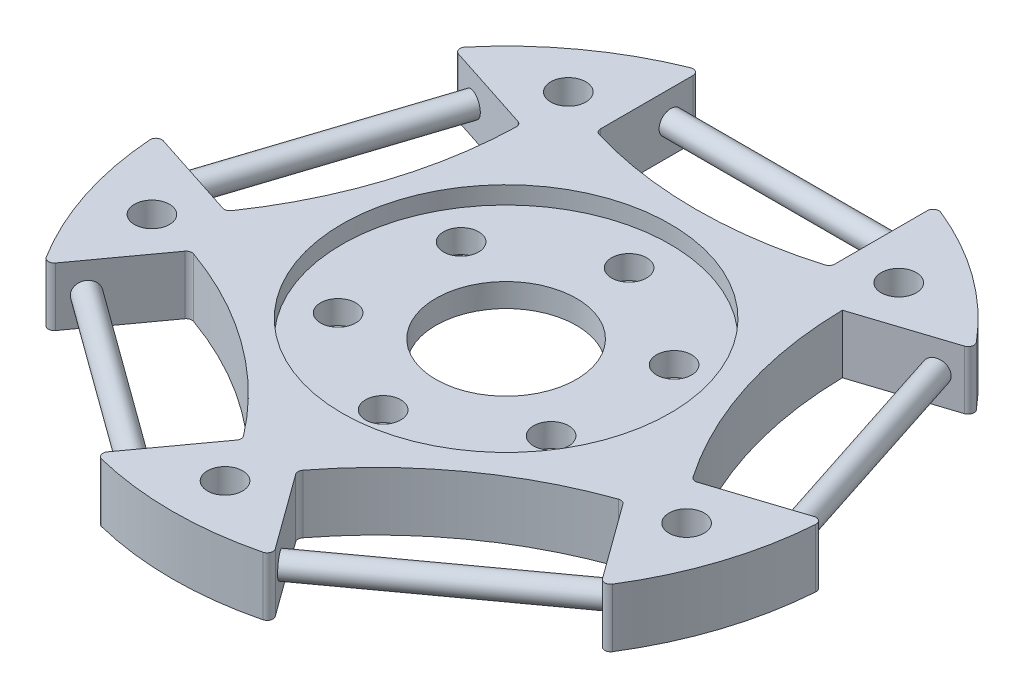
SolidWorks part; units mm, degrees
other "Camera1"
ref_plane "Front Plane" through (0, 0, 0) normal (0, 0, 1) x (1, 0, 0)
ref_plane "Top Plane" through (0, 0, 0) normal (0, 1, 0) x (1, 0, 0)
ref_plane "Right Plane" through (0, 0, 0) normal (1, 0, 0) x (0, 0, -1)
sketch "Sketch1" plane through (0, 0, 0) normal (0, 1, 0) x (1, 0, 0)
  line L0 (0, 0) -> (0, 50000) construction
  line L1 (0, 0) -> (-50000, 0) construction
  circle A0 centre (0, 0) radius 28.5
  dimension "D1" = 57
extrude "Boss-Extrude1" add sketch "Sketch1" along normal blind 5
sketch "Sketch2" plane through (0, 5, 0) normal (0, 1, 0) x (1, 0, 0)
  line L0 (0, 0) -> (13.4182, 0) construction
  line L1 (0, 0) -> (0, 50000) construction
  line L2 (10, 26.688) -> (10, 17.688)
  line L3 (-10, 26.688) -> (-10, 17.688)
  circle A0 centre (0, 0) radius 28.5 construction
  arc A1 (-10, 17.688) -> (10, 17.688) centre (0, 50.0973) ccw
  arc A2 (-10, 26.688) -> (10, 26.688) centre (0, 0) cw
  dimension "D1" = 9
  dimension "D2" = 10
extrude "Cut-Extrude1" cut sketch "Sketch2" against normal through all
pattern_circular "CirPattern1" count 5 over 360 about axis through (0, 0, 0) along (0, 1, 0) of "Cut-Extrude1"
sketch "Sketch3" plane through (0, 5, 0) normal (0, 1, 0) x (1, 0, 0)
  circle A0 centre (0, 0) radius 14
  dimension "D1" = 28
extrude "Cut-Extrude2" cut sketch "Sketch3" against normal blind 1.5
ref_plane "Plane1" through (0, 2.5, 0) normal (0, 1, 0) x (1, 0, 0)
mirror "Mirror1" about plane through (0, 2.5, 0) normal (0, 1, 0) of "Cut-Extrude2"
sketch "Sketch4" plane through (0, 3.5, 0) normal (0, 1, 0) x (1, 0, 0)
  circle A0 centre (0, 10.5) radius 1.5
  circle A1 centre (0, 0) radius 10.5 construction
  circle A2 centre (9.0933, 5.25) radius 1.5
  circle A3 centre (9.0933, -5.25) radius 1.5
  circle A4 centre (0, -10.5) radius 1.5
  circle A5 centre (-9.0933, -5.25) radius 1.5
  circle A6 centre (-9.0933, 5.25) radius 1.5
  circle A7 centre (0, 0) radius 6
  point P18 (0, 0)
  dimension "D2" = 3
  dimension "D4" = 12
  dimension "D1" = 10.5
  dimension "D3" = 6
extrude "Cut-Extrude3" cut sketch "Sketch4" against normal through all
sketch "Sketch5" plane through (0, 5, 0) normal (0, 1, 0) x (1, 0, 0)
  line L0 (0, 0) -> (0, -50000) construction
  circle A0 centre (0, -24) radius 1.5
  dimension "D1" = 24
extrude "Cut-Extrude4" cut sketch "Sketch5" against normal through all
pattern_circular "CirPattern2" count 5 over 360 about axis through (0, 0, 0) along (0, 1, 0) of "Cut-Extrude4"
fillet "Fillet1" radius 0.5 19 edges at (10, 2.5, -17.688) (-10, 2.5, -17.688) (-13.7321, 2.5, -14.9765) (-19.9125, 2.5, 4.0447) (-18.4869, 2.5, 8.4321) (-2.3066, 2.5, 20.1878) (19.9125, 2.5, 4.0447) (18.4869, 2.5, 8.4321) (2.3066, 2.5, 20.1878) (10, 2.5, -26.688) (22.2916, 2.5, -17.7576) (28.472, 2.5, 1.2635) (23.777, 2.5, 15.7132) (7.5967, 2.5, 27.4689) (-7.5967, 2.5, 27.4689) (-23.777, 2.5, 15.7132) (-28.472, 2.5, 1.2635) (-22.2916, 2.5, -17.7576) (-10, 2.5, -26.688)
sketch "Sketch7" plane through (-8.0902, 0, -5.8779) normal (0.809, 0, 0.5878) x (0.5878, 0, -0.809)
  line L1 (-33.8543, 2.5) -> (-18.0591, 2.5) construction
  line L3 (-18.0591, 0) -> (-18.0591, 5) construction
  line L5 (-22.0079, 10) -> (-22.0079, 0) construction
  line L7 (-18.0591, 0) -> (-25.9567, 0) construction
  circle A0 centre (-24.0591, 2.5) radius 1
  point P0 (-25.9567, 2.5)
  point P1 (-22.0079, 5)
  dimension "D1" = 2
  dimension "D2" = 6
extrude "Boss-Extrude2" add sketch "Sketch7" along normal up to next (20 mm away)
pattern_circular "CirPattern3" count 5 over 360 about axis through (0, 3.5, 0) along (0, 1, 0) of "Boss-Extrude2"
